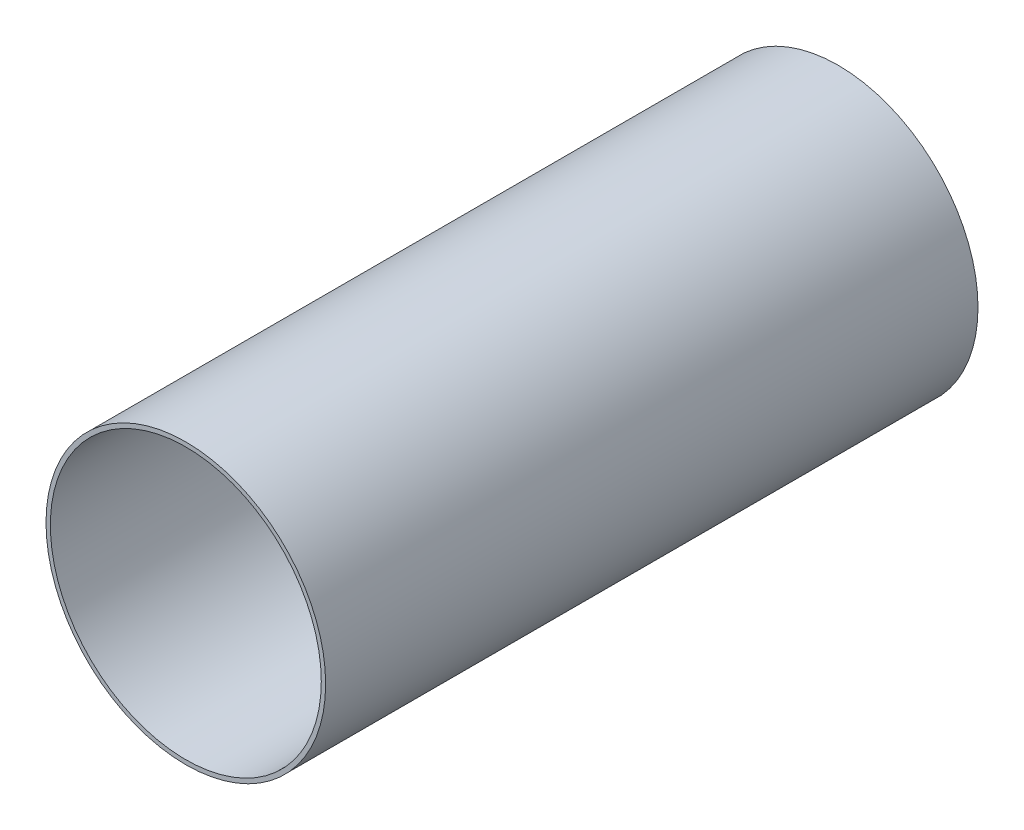
SolidWorks part; units mm, degrees
ref_plane "Plane1" through (0, 0, 0) normal (0, 0, 1) x (1, 0, 0)
ref_plane "Plane2" through (0, 0, 0) normal (0, 1, 0) x (1, 0, 0)
ref_plane "Plane3" through (0, 0, 0) normal (1, 0, 0) x (0, 0, -1)
sketch "Эскиз1" plane through (0, 0, 0) normal (0, 0, 1) x (1, 0, 0)
  circle A0 centre (689, 689) radius 643
  circle A1 centre (689, 689) radius 623
extrude "Вытянуть1" add sketch "Эскиз1" against normal blind 3000
